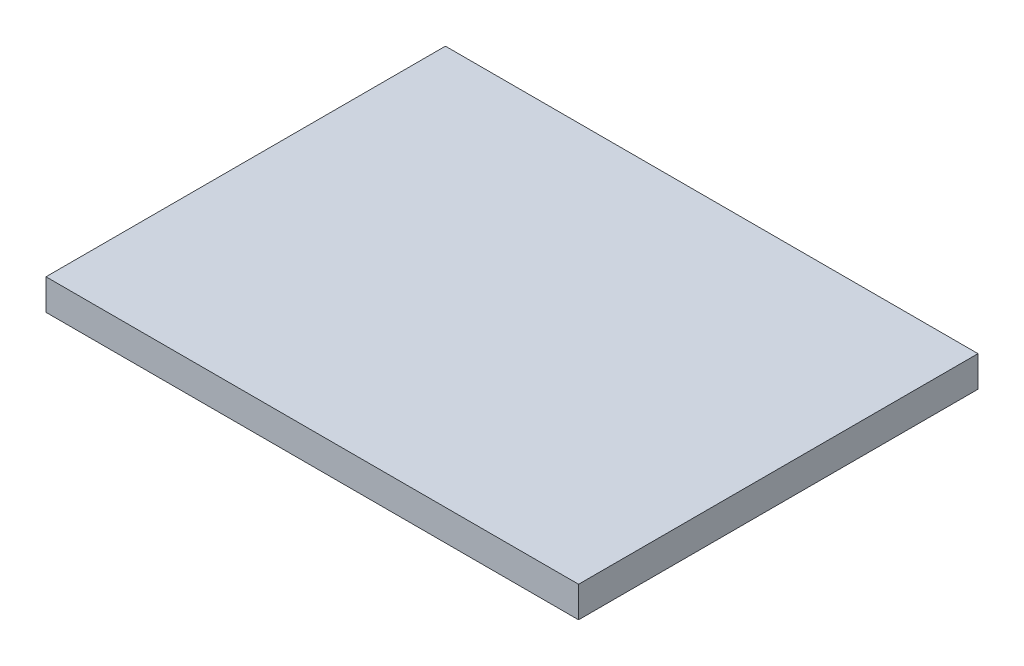
SolidWorks part; units mm, degrees
ref_plane "Front" through (0, 0, 0) normal (0, 0, 1) x (1, 0, 0)
ref_plane "Top" through (0, 0, 0) normal (0, 1, 0) x (1, 0, 0)
ref_plane "Right" through (0, 0, 0) normal (1, 0, 0) x (0, 0, -1)
sketch "Sketch1" plane through (0, 0, 0) normal (0, 1, 0) x (1, 0, 0)
  line L1 (0, 0) -> (42.667, 0)
  line L2 (0, 0) -> (0, -32)
  line L3 (0, -32) -> (42.667, -32)
  line L4 (42.667, 0) -> (42.667, -32)
  dimension "D1" = 42.667
  dimension "D2" = 32
extrude "Extrude1" add sketch "Sketch1" along normal blind 2
sketch "Sketch2" plane through (0, 2, 0) normal (0, 1, 0) x (-1, 0, 0)
  line L0 (-4.0615, 28.954) -> (0, 32) construction
  line L1 (-4.0615, 3.046) -> (-38.6055, 3.046)
  line L2 (-4.0615, 3.046) -> (-4.0615, 28.954)
  line L3 (-4.0615, 28.954) -> (-38.6055, 28.954)
  line L4 (-38.6055, 3.046) -> (-38.6055, 28.954)
  line L5 (-38.6055, 3.046) -> (-42.667, 0) construction
  dimension "D1" = 34.544
  dimension "D2" = 25.908
extrude "Cut-Extrude3" cut sketch "Sketch2" against normal through all flip side to cut
